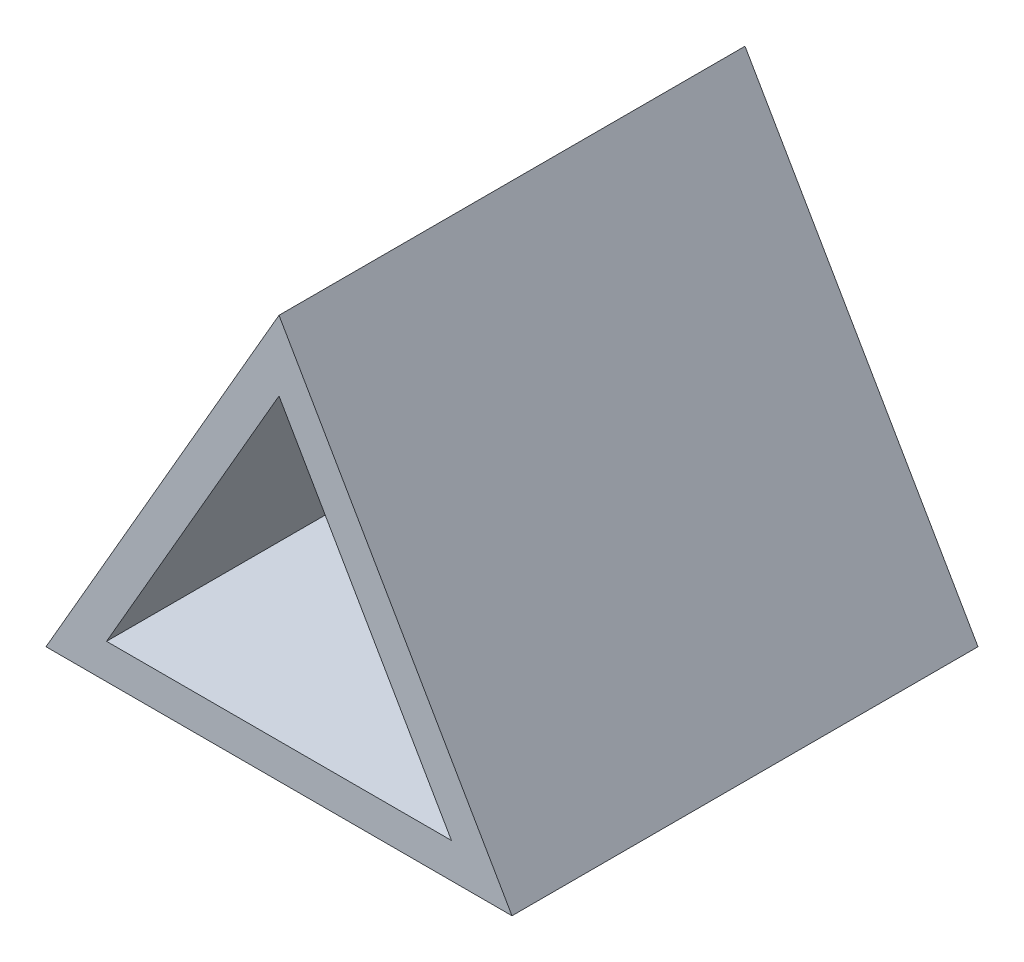
SolidWorks part; units mm, degrees
ref_plane "前视基准面" through (0, 0, 0) normal (0, 0, 1) x (1, 0, 0)
ref_plane "上视基准面" through (0, 0, 0) normal (0, 1, 0) x (1, 0, 0)
ref_plane "右视基准面" through (0, 0, 0) normal (1, 0, 0) x (0, 0, -1)
other "Configuration Table"
sketch "草图1" plane through (0, 0, 0) normal (0, 0, 1) x (1, 0, 0)
  line L0 (9.5634, 43.5086) -> (-10.4366, 8.8676)
  line L1 (-10.4366, 8.8676) -> (29.5634, 8.8676)
  line L2 (29.5634, 8.8676) -> (9.5634, 43.5086)
  point P2 (-3.0716, 25.3833)
  dimension "D1" = 60
  dimension "D2" = 60
  dimension "D3" = 40
extrude "凸台-拉伸1" add sketch "草图1" along normal blind 40
sketch "草图2" plane through (0, 0, 40) normal (0, 0, 1) x (1, 0, 0)
  line L0 (9.5634, 43.5086) -> (-10.4366, 8.8676) construction
  line L1 (-10.4366, 8.8676) -> (29.5634, 8.8676) construction
  line L2 (29.5634, 8.8676) -> (9.5634, 43.5086) construction
  line L3 (9.5634, 37.5086) -> (-5.2405, 11.8676)
  line L4 (-5.2405, 11.8676) -> (24.3672, 11.8676)
  line L5 (24.3672, 11.8676) -> (9.5634, 37.5086)
  dimension "D1" = 3
extrude "切除-拉伸1" cut sketch "草图2" against normal blind 37
